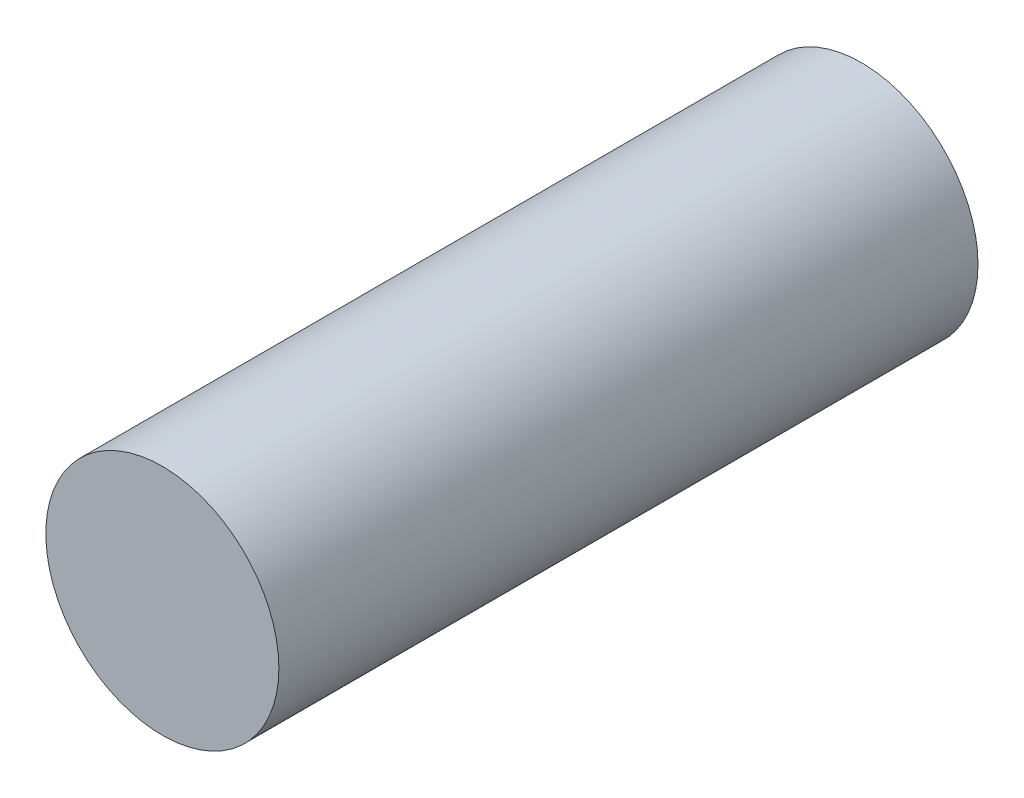
SolidWorks part; units mm, degrees
ref_plane "Front Plane" through (0, 0, 0) normal (0, 0, 1) x (1, 0, 0)
ref_plane "Top Plane" through (0, 0, 0) normal (0, 1, 0) x (1, 0, 0)
ref_plane "Right Plane" through (0, 0, 0) normal (1, 0, 0) x (0, 0, -1)
sketch "Sketch1" plane through (0, 0, 0) normal (0, 0, 1) x (1, 0, 0)
  circle A0 centre (0, 0) radius 5
extrude "Boss-Extrude1" add sketch "Sketch1" along normal blind 30
